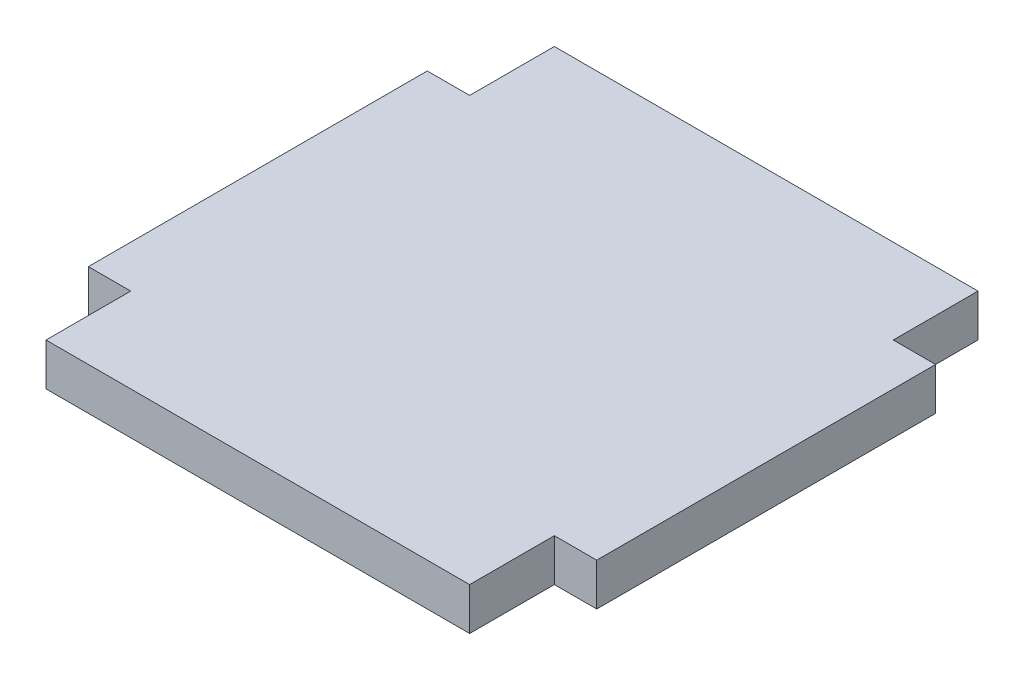
SolidWorks part; units mm, degrees
ref_plane "Front Plane" through (0, 0, 0) normal (0, 0, 1) x (1, 0, 0)
ref_plane "Top Plane" through (0, 0, 0) normal (0, 1, 0) x (1, 0, 0)
ref_plane "Right Plane" through (0, 0, 0) normal (1, 0, 0) x (0, 0, -1)
sketch "Sketch1" plane through (0, 0, 0) normal (0, 1, 0) x (1, 0, 0)
  line L1 (0, 0) -> (38.1, 0)
  line L2 (0, 0) -> (0, 38.1)
  line L3 (0, 38.1) -> (38.1, 38.1)
  line L4 (38.1, 0) -> (38.1, 38.1)
  dimension "D1" = 38.1
  dimension "D2" = 38.1
extrude "Boss-Extrude1" add sketch "Sketch1" along normal blind 3.175
sketch "Sketch2" plane through (0, 0, 0) normal (0, -1, 0) x (1, 0, 0)
  line L1 (38.1, -38.1) -> (34.925, -38.1)
  line L2 (38.1, -38.1) -> (38.1, -31.75)
  line L3 (38.1, -31.75) -> (34.925, -31.75)
  line L4 (34.925, -38.1) -> (34.925, -31.75)
  line L5 (38.1, 0) -> (34.925, 0)
  line L6 (38.1, 0) -> (38.1, -6.35)
  line L7 (38.1, -6.35) -> (34.925, -6.35)
  line L8 (34.925, 0) -> (34.925, -6.35)
  line L9 (0, -38.1) -> (3.175, -38.1)
  line L10 (0, -38.1) -> (0, -31.75)
  line L11 (0, -31.75) -> (3.175, -31.75)
  line L12 (3.175, -38.1) -> (3.175, -31.75)
  line L13 (0, 0) -> (3.175, 0)
  line L14 (0, 0) -> (0, -6.35)
  line L15 (0, -6.35) -> (3.175, -6.35)
  line L16 (3.175, 0) -> (3.175, -6.35)
  dimension "D1" = 6.35
  dimension "D2" = 6.35
  dimension "D3" = 3.175
  dimension "D4" = 3.175
extrude "Cut-Extrude1" cut sketch "Sketch2" against normal blind 3.175
